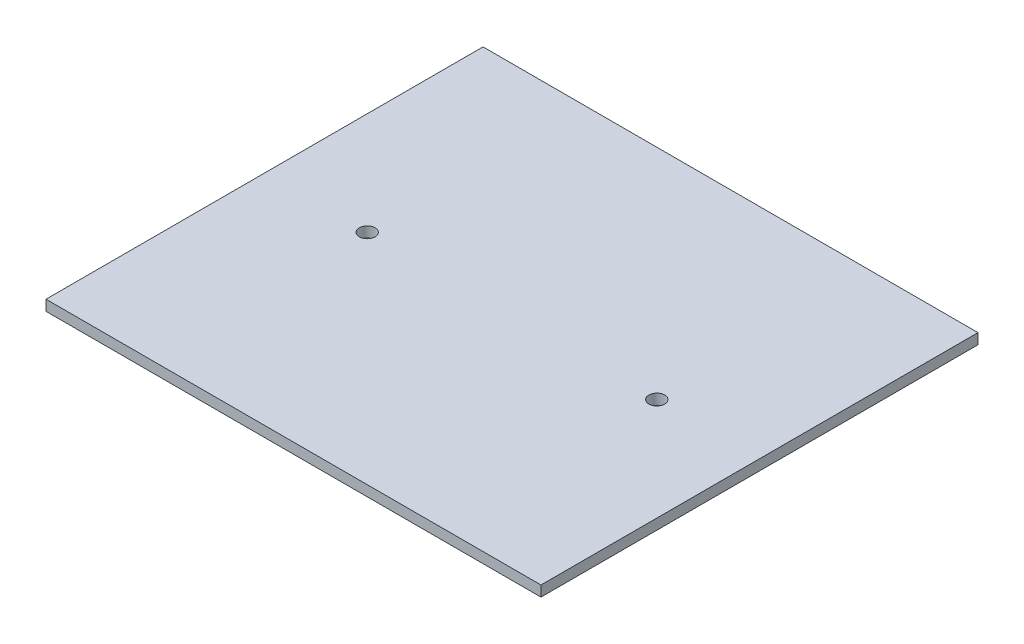
SolidWorks part; units mm, degrees
ref_plane "Front Plane" through (0, 0, 0) normal (0, 0, 1) x (1, 0, 0)
ref_plane "Top Plane" through (0, 0, 0) normal (0, 1, 0) x (1, 0, 0)
ref_plane "Right Plane" through (0, 0, 0) normal (1, 0, 0) x (0, 0, -1)
sketch "Sketch1" plane through (0, 0, 0) normal (0, 1, 0) x (1, 0, 0)
  line L1 (-47, -41.5) -> (47, -41.5)
  line L2 (-47, -41.5) -> (-47, 41.5)
  line L3 (-47, 41.5) -> (47, 41.5)
  line L4 (47, -41.5) -> (47, 41.5)
  line L5 (-47, -41.5) -> (47, 41.5) construction
  line L6 (-47, 41.5) -> (47, -41.5) construction
  line L7 (-42, -36.5) -> (42, -36.5) construction
  line L8 (-42, -36.5) -> (-42, 36.5) construction
  line L9 (-42, 36.5) -> (42, 36.5) construction
  line L10 (42, -36.5) -> (42, 36.5) construction
  line L11 (-42, -36.5) -> (42, 36.5) construction
  line L12 (-42, 36.5) -> (42, -36.5) construction
  point P0 (0, 0)
  point P14 (0, 0)
  point P19 (0, 0)
  dimension "D1" = 83
  dimension "D2" = 94
  dimension "D4" = 5
  dimension "D5" = 5
extrude "Boss-Extrude1" add sketch "Sketch1" along normal blind 2
sketch "Sketch2" plane through (0, 2, 0) normal (0, 1, 0) x (1, 0, 0)
  line L0 (0, 41.5) -> (0, -41.5) construction
  line L1 (47, 41.5) -> (-47, 41.5) construction
  line L2 (-47, -41.5) -> (47, -41.5) construction
  circle A0 centre (27.5, 0) radius 1.5
  circle A1 centre (-27.5, 0) radius 1.5
  dimension "D1" = 3
  dimension "D2" = 27.5
  dimension "D3" = 41.5
extrude "Cut-Extrude1" cut sketch "Sketch2" against normal through all
equation "\"D5@Sketch1\"=\"D4@Sketch1\""
